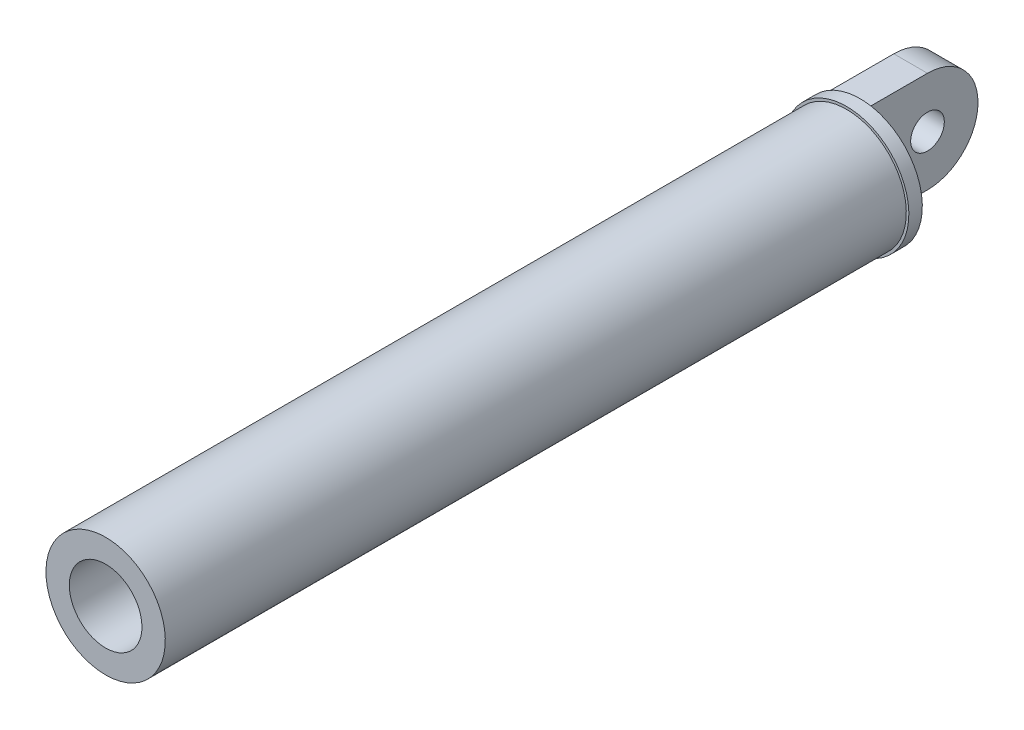
SolidWorks part; units mm, degrees
ref_plane "Front Plane" through (0, 0, 0) normal (0, 0, 1) x (1, 0, 0)
ref_plane "Top Plane" through (0, 0, 0) normal (0, 1, 0) x (1, 0, 0)
ref_plane "Right Plane" through (0, 0, 0) normal (1, 0, 0) x (0, 0, -1)
sketch "Sketch1" plane through (0, 0, 0) normal (1, 0, 0) x (0, 0, -1)
  line L1 (0, 15) -> (-20, 15)
  line L3 (0, -15) -> (-20, -15)
  line L4 (-20, 15) -> (-20, -15)
  circle A0 centre (0, 0) radius 5
  arc A2 (0, -15) -> (0, 15) centre (0, 0) ccw
  dimension "D1" = 10
  dimension "D2" = 30
  dimension "D3" = 20
extrude "Boss-Extrude1" add sketch "Sketch1" along normal mid plane 10
sketch "Sketch3" plane through (5, 0, 0) normal (1, 0, 0) x (0, 0, -1)
  line L0 (-20, 15) -> (-20, 18.4759)
  line L1 (-20, 18.4759) -> (-24, 18.4759)
  line L2 (-24, 18.4759) -> (-24, 17.7135)
  line L3 (-24, 17.7135) -> (-244, 17.7135)
  line L4 (-244, 17.7135) -> (-244, 10.7822)
  line L5 (-244, 10.7822) -> (-26, 10.7822)
  line L6 (-26, 10.7822) -> (-26, 0)
  line L7 (-26, 0) -> (-20, 0)
  line L8 (-20, 15) -> (-20, -15) construction
  line L9 (-20, 1.817) -> (-20, 15.4857)
  line L10 (-20, 0) -> (-20, 1.817)
  dimension "D1" = 6
  dimension "D2" = 2
  dimension "D3" = 220
revolve "Revolve1" add sketch "Sketch3" angle 360 about L7
